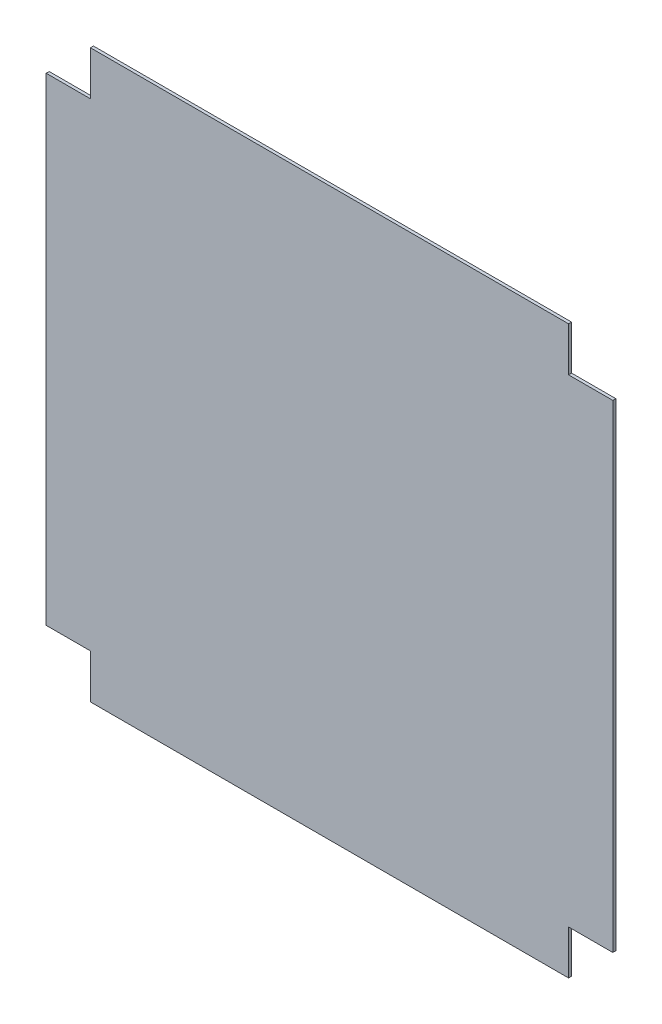
SolidWorks part; units mm, degrees
ref_plane "前基準面" through (0, 0, 0) normal (0, 0, 1) x (1, 0, 0)
ref_plane "上基準面" through (0, 0, 0) normal (0, 1, 0) x (1, 0, 0)
ref_plane "右基準面" through (0, 0, 0) normal (1, 0, 0) x (0, 0, -1)
sketch "草圖1" plane through (0, 0, 0) normal (0, 0, 1) x (1, 0, 0)
  line L1 (-80.933, 58.7954) -> (157.067, 58.7954)
  line L2 (-102.933, 36.7954) -> (-102.933, -201.2046)
  line L3 (-80.933, -223.2046) -> (157.067, -223.2046)
  line L4 (179.067, 36.7954) -> (179.067, -201.2046)
  line L7 (-102.933, 36.7954) -> (-80.933, 36.7954)
  line L8 (-80.933, 58.7954) -> (-80.933, 36.7954)
  line L11 (-102.933, -201.2046) -> (-80.933, -201.2046)
  line L12 (-80.933, -223.2046) -> (-80.933, -201.2046)
  line L15 (179.067, -201.2046) -> (157.067, -201.2046)
  line L16 (157.067, -223.2046) -> (157.067, -201.2046)
  line L19 (179.067, 36.7954) -> (157.067, 36.7954)
  line L20 (157.067, 58.7954) -> (157.067, 36.7954)
  dimension "D3" = 22
  dimension "D4" = 22
  dimension "D5" = 22
  dimension "D6" = 22
  dimension "D7" = 22
  dimension "D8" = 22
  dimension "D9" = 22
  dimension "D10" = 22
extrude "填料-伸長1" add sketch "草圖1" along normal blind 1.5
